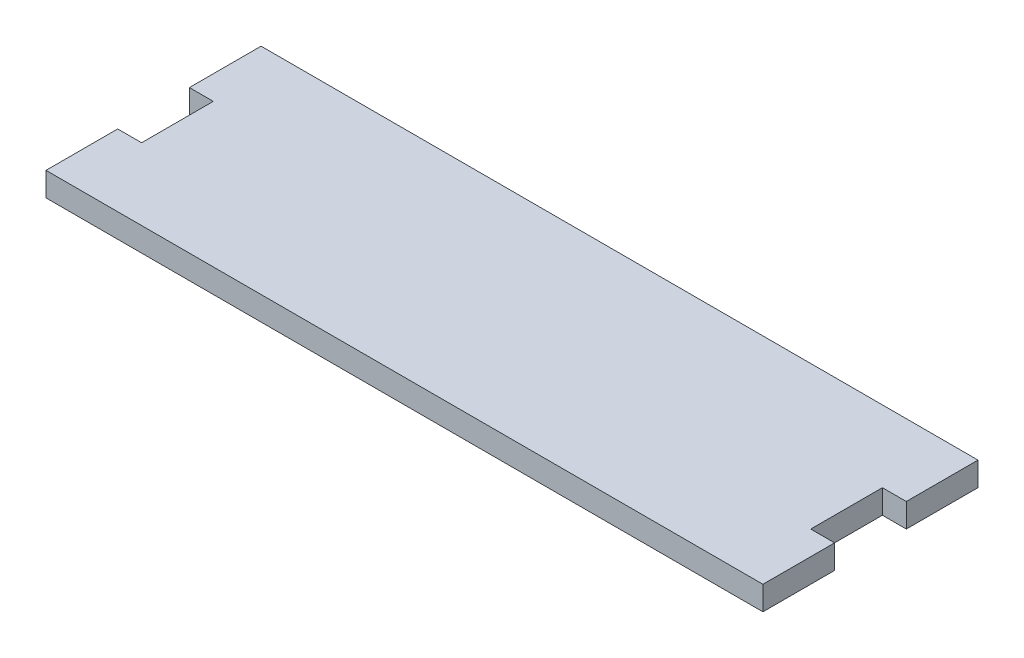
SolidWorks part; units mm, degrees
ref_plane "前视基准面" through (0, 0, 0) normal (0, 0, 1) x (1, 0, 0)
ref_plane "上视基准面" through (0, 0, 0) normal (0, 1, 0) x (1, 0, 0)
ref_plane "右视基准面" through (0, 0, 0) normal (1, 0, 0) x (0, 0, -1)
sketch "草图1" plane through (0, 0, 0) normal (0, 1, 0) x (1, 0, 0)
  line L1 (-70, 22.5) -> (70, 22.5)
  line L2 (-70, 22.5) -> (-70, -22.5)
  line L3 (-70, -22.5) -> (70, -22.5)
  line L4 (70, 22.5) -> (70, -22.5)
  line L5 (-70, 22.5) -> (70, -22.5) construction
  line L6 (-70, -22.5) -> (70, 22.5) construction
  line L7 (-70, 22.5) -> (-75, 22.5)
  line L8 (-70, 22.5) -> (-70, 7.5)
  line L9 (-70, 7.5) -> (-75, 7.5)
  line L10 (-75, 22.5) -> (-75, 7.5)
  line L11 (-70, -22.5) -> (-75, -22.5)
  line L12 (-70, -22.5) -> (-70, -7.5)
  line L13 (-70, -7.5) -> (-75, -7.5)
  line L14 (-75, -22.5) -> (-75, -7.5)
  line L15 (70, 22.5) -> (75, 22.5)
  line L16 (70, 22.5) -> (70, 7.5)
  line L17 (70, 7.5) -> (75, 7.5)
  line L18 (75, 22.5) -> (75, 7.5)
  line L19 (70, -22.5) -> (75, -22.5)
  line L20 (70, -22.5) -> (70, -7.5)
  line L21 (70, -7.5) -> (75, -7.5)
  line L22 (75, -22.5) -> (75, -7.5)
  point P0 (0, 0)
  dimension "D1" = 140
  dimension "D2" = 45
  dimension "D3" = 15
  dimension "D4" = 5
  dimension "D5" = 15
  dimension "D6" = 5
  dimension "D7" = 5
  dimension "D8" = 5
  dimension "D9" = 15
  dimension "D10" = 15
extrude "凸台-拉伸1" add sketch "草图1" along normal blind 5 contours L4 L1 L2 L3 | L7 L10 L9 L2 | L14 L11 L2 L13 | L18 L15 L4 L17 | L19 L22 L21 L4
